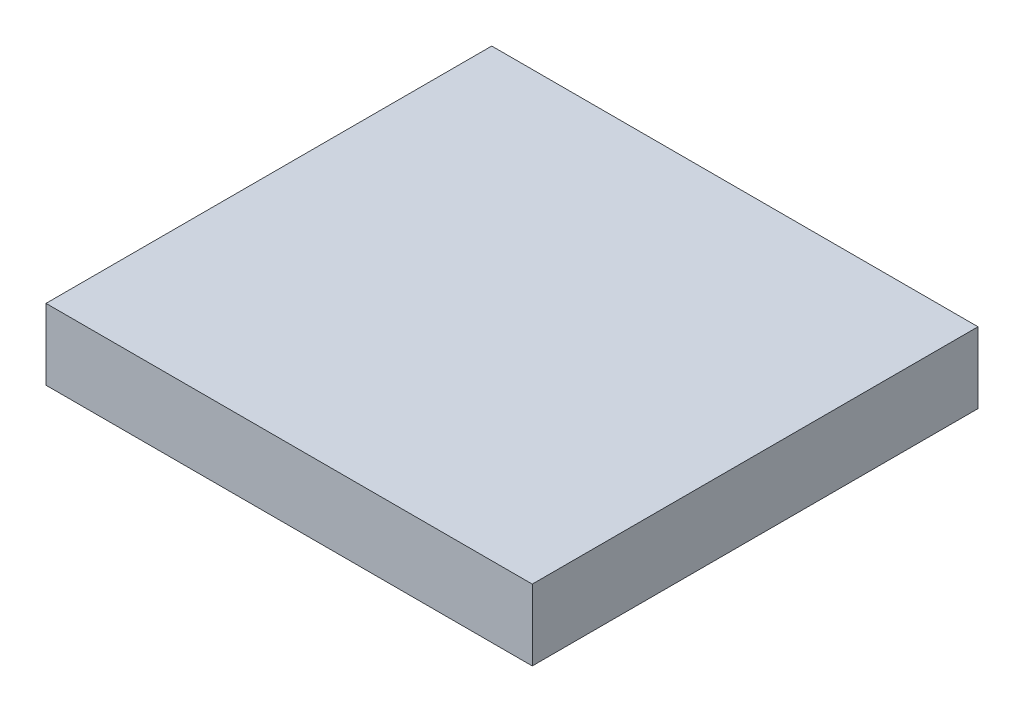
SolidWorks part; units mm, degrees
ref_plane "Front Plane" through (0, 0, 0) normal (0, 0, 1) x (1, 0, 0)
ref_plane "Top Plane" through (0, 0, 0) normal (0, 1, 0) x (1, 0, 0)
ref_plane "Right Plane" through (0, 0, 0) normal (1, 0, 0) x (0, 0, -1)
sketch "Sketch1" plane through (0, 0, 0) normal (0, 1, 0) x (1, 0, 0)
  line L1 (0, 0) -> (304.8, 0)
  line L2 (0, 0) -> (0, 279.4)
  line L3 (0, 279.4) -> (304.8, 279.4)
  line L4 (304.8, 0) -> (304.8, 279.4)
  dimension "D1" = 304.8
  dimension "D2" = 279.4
extrude "Boss-Extrude1" add sketch "Sketch1" along normal blind 44.45
